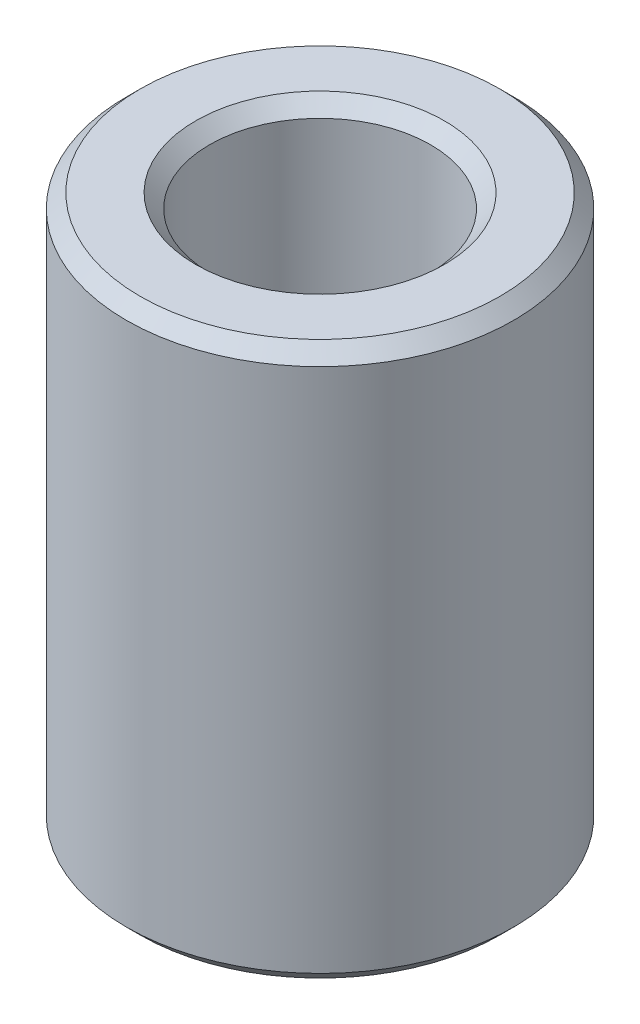
SolidWorks part; units mm, degrees
ref_plane "Alzado" through (0, 0, 0) normal (0, 0, 1) x (1, 0, 0)
ref_plane "Planta" through (0, 0, 0) normal (0, 1, 0) x (1, 0, 0)
ref_plane "Vista lateral" through (0, 0, 0) normal (1, 0, 0) x (0, 0, -1)
sketch "Croquis1" plane through (0, 0, 0) normal (0, 1, 0) x (1, 0, 0)
  circle A0 centre (0, 0) radius 7
  circle A1 centre (0, 0) radius 4
  dimension "D1" = 14
  dimension "D2" = 8
extrude "Saliente-Extruir1" add sketch "Croquis1" along normal blind 20
chamfer "Chaflán1" distance 0.5 angle 45 4 edges at (0, 0, 7) (0, 20, 7) (0, 0, 4) (0, 20, 4)
